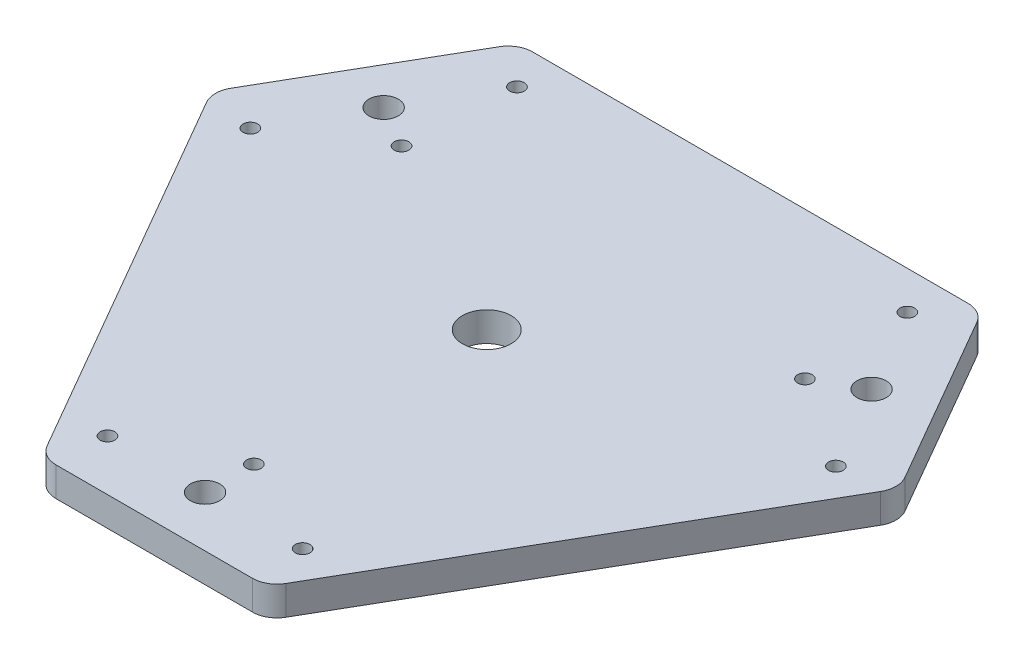
SolidWorks part; units mm, degrees
ref_plane "Front Plane" through (0, 0, 0) normal (0, 0, 1) x (1, 0, 0)
ref_plane "Top Plane" through (0, 0, 0) normal (0, 1, 0) x (1, 0, 0)
ref_plane "Right Plane" through (0, 0, 0) normal (1, 0, 0) x (0, 0, -1)
sketch "Sketch1" plane through (0, 0, 0) normal (0, 1, 0) x (1, 0, 0)
  line L0 (-47.5, 54) -> (47.5, 54)
  line L8 (47.5, 54) -> (70.5154, 14.1362)
  line L9 (70.5154, 14.1362) -> (23.0154, -68.1362)
  line L10 (23.0154, -68.1362) -> (-23.0154, -68.1362)
  line L11 (-23.0154, -68.1362) -> (-70.5154, 14.1362)
  line L12 (-70.5154, 14.1362) -> (-47.5, 54)
  circle A0 centre (0, 0) radius 54 construction
  point P9 (0, 54)
  point P10 (0, -68.1362)
  dimension "D1" = 95
  dimension "D2" = 54
extrude "Boss-Extrude1" add sketch "Sketch1" along normal blind 6
sketch "Sketch2" plane through (0, 6, 0) normal (0, 1, 0) x (1, 0, 0)
  line L0 (47.5, 54) -> (-47.5, 54) construction
  line L1 (50, 28.8675) -> (-50, 28.8675) construction
  line L2 (-50, 28.8675) -> (0, -57.735) construction
  line L3 (0, -57.735) -> (50, 28.8675) construction
  line L4 (0, -68.1362) -> (0, -37.1505) construction
  line L5 (-23.0154, -68.1362) -> (23.0154, -68.1362) construction
  circle A0 centre (0, 0) radius 28.8675 construction
  circle A1 centre (50, 28.8675) radius 3
  circle A2 centre (-50, 28.8675) radius 3
  circle A3 centre (0, -57.735) radius 3
  circle A4 centre (-20, -57.735) radius 1.5
  circle A5 centre (20, -57.735) radius 1.5
  circle A6 centre (0, -47.735) radius 1.5
  circle A7 centre (-60, 11.547) radius 1.5
  circle A8 centre (-41.3397, 23.8675) radius 1.5
  circle A9 centre (-40, 46.188) radius 1.5
  circle A10 centre (40, 46.188) radius 1.5
  circle A11 centre (41.3397, 23.8675) radius 1.5
  circle A12 centre (60, 11.547) radius 1.5
  point P36 (0, 0)
  dimension "D1" = 6
  dimension "D3" = 3
  dimension "D2" = 100
  dimension "D4" = 10
  dimension "D5" = 40
  dimension "D6" = 3
extrude "Cut-Extrude1" cut sketch "Sketch2" against normal through all
fillet "Fillet1" radius 5 6 edges at (-70.5154, 3, -14.1362) (-47.5, 3, -54) (47.5, 3, -54) (70.5154, 3, -14.1362) (-23.0154, 3, 68.1362) (23.0154, 3, 68.1362)
sketch "Sketch4" plane through (0, 6, 0) normal (0, 1, 0) x (1, 0, 0)
  circle A0 centre (0, 0) radius 5
  dimension "D1" = 10
extrude "Cut-Extrude3" cut sketch "Sketch4" against normal through all
